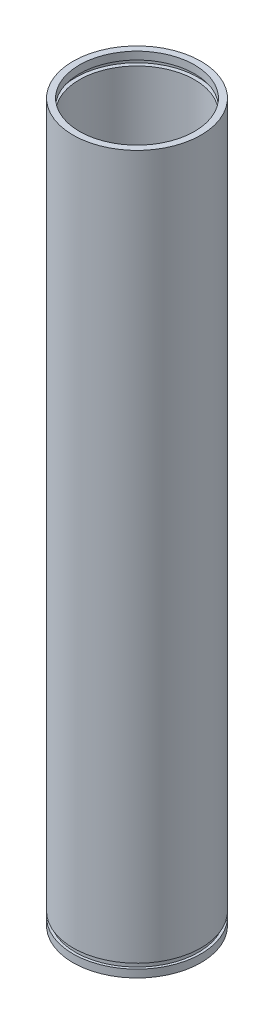
SolidWorks part; units mm, degrees
ref_plane "Front Plane" through (0, 0, 0) normal (0, 0, 1) x (1, 0, 0)
ref_plane "Top Plane" through (0, 0, 0) normal (0, 1, 0) x (1, 0, 0)
ref_plane "Right Plane" through (0, 0, 0) normal (1, 0, 0) x (0, 0, -1)
sketch "Sketch1" plane through (0, 0, 0) normal (0, 1, 0) x (1, 0, 0)
  circle A0 centre (0, 0) radius 22.5
  circle A1 centre (0, 0) radius 25
extrude "Boss-Extrude1" add sketch "Sketch1" along normal blind 280
sketch "Sketch2" plane through (0, 0, 0) normal (0, 0, 1) x (1, 0, 0)
  line L0 (24, 275) -> (22.5, 275)
  line L1 (22.5, 0) -> (22.5, 280) construction
  line L2 (22.5, 277) -> (24, 277)
  line L3 (24, 277) -> (24, 275)
  line L4 (22.5, 277) -> (22.1571, 277)
  line L5 (22.1571, 277) -> (22.1571, 275)
  line L6 (22.1571, 275) -> (22.5, 275)
  line L7 (0, 307.215) -> (0, -29.2818) construction
  line L8 (22.5, 8) -> (24, 8)
  line L9 (24, 8) -> (24, 10)
  line L10 (24, 10) -> (21.7491, 10)
  line L11 (21.7491, 10) -> (21.7491, 8)
  line L12 (21.7491, 8) -> (22.5, 8)
  line L13 (25, 0) -> (25, 280) construction
  line L14 (25, 3) -> (24, 3)
  line L15 (24, 3) -> (24, 5)
  line L16 (24, 5) -> (25.3766, 5)
  line L17 (25.3766, 5) -> (25.3766, 3)
  line L18 (25.3766, 3) -> (25, 3)
revolve "Cut-Revolve1" cut sketch "Sketch2" angle 360 about L7
